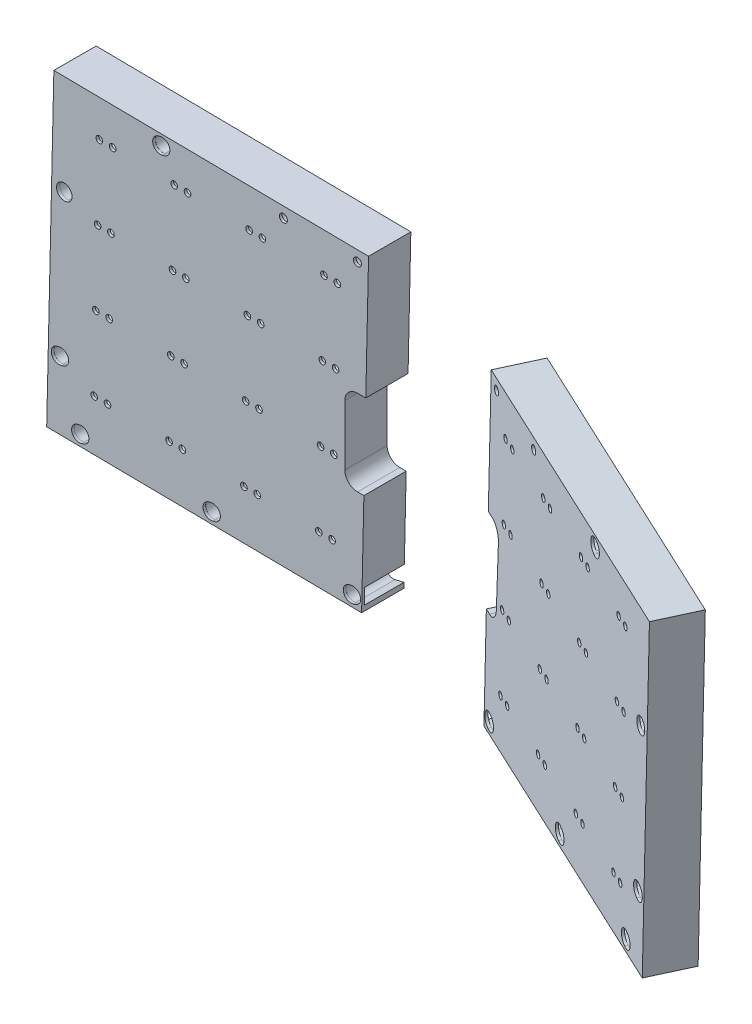
SolidWorks part; units mm, degrees
ref_plane "Front Plane" through (0, 0, 0) normal (0, 0, 1) x (1, 0, 0)
ref_plane "Top Plane" through (0, 0, 0) normal (0, 1, 0) x (1, 0, 0)
ref_plane "Right Plane" through (0, 0, 0) normal (1, 0, 0) x (0, 0, -1)
sketch "Sketch1" plane through (0, 0, 0) normal (0, 0, 1) x (1, 0, 0)
  line L11 (99.4099, -219.1387) -> (-89.6592, -216.966)
  line L12 (-89.6592, -216.966) -> (-93.9705, -404.5237)
  line L13 (-93.9705, -404.5237) -> (95.2285, -406.698)
  line L14 (95.2285, -406.698) -> (99.4099, -219.1387)
  line L21 (95.5423, -393.9824) -> (99.1392, -231.8547)
  line L22 (95.2501, -406.6982) -> (95.5423, -393.9824)
  line L23 (-93.9489, -404.524) -> (95.2501, -406.6982)
  line L24 (-89.6377, -216.9662) -> (-93.9489, -404.524)
  line L25 (99.4315, -219.139) -> (-89.6377, -216.9662)
  line L26 (99.1392, -231.8547) -> (99.4315, -219.139)
  line L27 (95.5423, -393.9824) -> (99.1392, -231.8547)
  line L28 (95.2501, -406.6982) -> (95.5423, -393.9824)
  line L29 (-93.9489, -404.524) -> (95.2501, -406.6982)
  line L30 (-89.6377, -216.9662) -> (-93.9489, -404.524)
  line L31 (99.4315, -219.139) -> (-89.6377, -216.9662)
  line L32 (99.1392, -231.8547) -> (99.4315, -219.139)
  circle A0 centre (80.6426, -242.5843) radius 2 construction
  circle A1 centre (72.6447, -242.4004) radius 2 construction
  circle A2 centre (35.6545, -241.5501) radius 2 construction
  circle A3 centre (27.6566, -241.3663) radius 2 construction
  circle A4 centre (-9.3336, -240.516) radius 2 construction
  circle A5 centre (-17.3315, -240.3322) radius 2 construction
  circle A6 centre (-54.3218, -239.4819) radius 2 construction
  circle A7 centre (-62.3197, -239.2981) radius 2 construction
  circle A8 centre (-63.3538, -284.2862) radius 2 construction
  circle A9 centre (-55.3559, -284.47) radius 2 construction
  circle A10 centre (-18.3657, -285.3203) radius 2 construction
  circle A11 centre (-10.3678, -285.5041) radius 2 construction
  circle A12 centre (26.6225, -286.3544) radius 2 construction
  circle A13 centre (34.6204, -286.5383) radius 2 construction
  circle A14 centre (71.6106, -287.3885) radius 2 construction
  circle A15 centre (79.6085, -287.5724) radius 2 construction
  circle A16 centre (78.5744, -332.5605) radius 2 construction
  circle A17 centre (70.5765, -332.3767) radius 2 construction
  circle A18 centre (33.5862, -331.5264) radius 2 construction
  circle A19 centre (25.5883, -331.3425) radius 2 construction
  circle A20 centre (-11.4019, -330.4923) radius 2 construction
  circle A21 centre (-19.3998, -330.3084) radius 2 construction
  circle A22 centre (-56.39, -329.4581) radius 2 construction
  circle A23 centre (-64.3879, -329.2743) radius 2 construction
  circle A24 centre (-65.422, -374.2624) radius 2 construction
  circle A25 centre (-57.4241, -374.4463) radius 2 construction
  circle A26 centre (-20.4339, -375.2965) radius 2 construction
  circle A27 centre (-12.436, -375.4804) radius 2 construction
  circle A28 centre (24.5542, -376.3307) radius 2 construction
  circle A29 centre (32.5521, -376.5145) radius 2 construction
  circle A30 centre (69.5424, -377.3648) radius 2 construction
  circle A31 centre (77.5402, -377.5486) radius 2 construction
  circle A32 centre (80.6426, -242.5843) radius 2
  circle A33 centre (72.6447, -242.4004) radius 2
  circle A34 centre (35.6545, -241.5501) radius 2
  circle A35 centre (27.6566, -241.3663) radius 2
  circle A36 centre (-9.3336, -240.516) radius 2
  circle A37 centre (-17.3315, -240.3322) radius 2
  circle A38 centre (-54.3218, -239.4819) radius 2
  circle A39 centre (-62.3197, -239.2981) radius 2
  circle A40 centre (-63.3538, -284.2862) radius 2
  circle A41 centre (-55.3559, -284.47) radius 2
  circle A42 centre (-18.3657, -285.3203) radius 2
  circle A43 centre (-10.3678, -285.5041) radius 2
  circle A44 centre (26.6225, -286.3544) radius 2
  circle A45 centre (34.6204, -286.5383) radius 2
  circle A46 centre (71.6106, -287.3885) radius 2
  circle A47 centre (79.6085, -287.5724) radius 2
  circle A48 centre (78.5744, -332.5605) radius 2
  circle A49 centre (70.5765, -332.3767) radius 2
  circle A50 centre (33.5862, -331.5264) radius 2
  circle A51 centre (25.5883, -331.3425) radius 2
  circle A52 centre (-11.4019, -330.4923) radius 2
  circle A53 centre (-19.3998, -330.3084) radius 2
  circle A54 centre (-56.39, -329.4581) radius 2
  circle A55 centre (-64.3879, -329.2743) radius 2
  circle A56 centre (-65.422, -374.2624) radius 2
  circle A57 centre (-57.4241, -374.4463) radius 2
  circle A58 centre (-20.4339, -375.2965) radius 2
  circle A59 centre (-12.436, -375.4804) radius 2
  circle A60 centre (24.5542, -376.3307) radius 2
  circle A61 centre (32.5521, -376.5145) radius 2
  circle A62 centre (69.5424, -377.3648) radius 2
  circle A63 centre (77.5402, -377.5486) radius 2
  ellipse E1 centre (-25.651, -224.0611) end of major axis (-30.0544, -225.5074) minor radius 4.572 construction
  ellipse E2 centre (48.2624, -224.9105) end of major axis (49.7684, -226.8033) minor radius 2.413 construction
  ellipse E3 centre (92.7518, -225.4218) end of major axis (94.2578, -227.3145) minor radius 2.413 construction
  ellipse E4 centre (88.9025, -400.2657) end of major axis (84.3472, -401.3501) minor radius 4.572 construction
  ellipse E5 centre (4.628, -399.2972) end of major axis (0.0728, -400.3817) minor radius 4.572 construction
  ellipse E6 centre (-86.5199, -363.9081) end of major axis (-91.0751, -364.9925) minor radius 4.572 construction
  ellipse E7 centre (-74.3216, -398.39) end of major axis (-78.8768, -399.4744) minor radius 4.572 construction
  ellipse E9 centre (-25.651, -224.0611) end of major axis (-30.0544, -225.5074) minor radius 4.572
  ellipse E10 centre (48.2624, -224.9105) end of major axis (49.7684, -226.8033) minor radius 2.413
  ellipse E11 centre (92.7518, -225.4218) end of major axis (94.2578, -227.3145) minor radius 2.413
  ellipse E12 centre (88.9025, -400.2657) end of major axis (84.3472, -401.3501) minor radius 4.572
  ellipse E13 centre (4.628, -399.2972) end of major axis (0.0728, -400.3817) minor radius 4.572
  ellipse E14 centre (-86.5199, -363.9081) end of major axis (-91.0751, -364.9925) minor radius 4.572
  ellipse E15 centre (-74.3216, -398.39) end of major axis (-78.8768, -399.4744) minor radius 4.572
  dimension "D1" = 0
extrude "Boss-Extrude1" add sketch "Sketch1" against normal blind 1.5875
ref_plane "Plane1" through (-93.9489, -404.524, 5) normal (-0.9999, 0.0115, 0) x (0, 0, 1)
ref_plane "Plane2" through (158.3388, -225.7752, 115.9625) normal (-0.2101, -0.05, 0.9764) x (0.9777, -0.0108, 0.2099)
sketch "Sketch5" plane through (0, 0, -1.5875) normal (0, 0, -1) x (-1, 0, 0)
  line L0 (65.422, -374.2624) -> (57.4241, -374.4463) construction
  line L1 (65.5369, -379.2624) -> (57.539, -379.4463)
  line L2 (65.3071, -369.2624) -> (57.3092, -369.4463)
  line L3 (20.4339, -375.2965) -> (12.436, -375.4804) construction
  line L4 (20.5488, -380.2965) -> (12.5509, -380.4804)
  line L5 (20.319, -370.2965) -> (12.3211, -370.4804)
  line L6 (-24.5542, -376.3307) -> (-32.5521, -376.5145) construction
  line L7 (-24.4393, -381.3307) -> (-32.4372, -381.5145)
  line L8 (-24.6692, -371.3307) -> (-32.6671, -371.5145)
  line L9 (-69.5424, -377.3648) -> (-77.5402, -377.5486) construction
  line L10 (-69.4274, -382.3648) -> (-77.4253, -382.5486)
  line L11 (-69.6573, -372.3648) -> (-77.6552, -372.5486)
  line L12 (64.3879, -329.2743) -> (56.39, -329.4581) construction
  line L13 (64.5028, -334.2746) -> (56.5049, -334.4585)
  line L14 (64.2729, -324.274) -> (56.2751, -324.4578)
  line L15 (19.3998, -330.3084) -> (11.4019, -330.4923) construction
  line L16 (19.5147, -335.3087) -> (11.5168, -335.4926)
  line L17 (19.2848, -325.3081) -> (11.2869, -325.4919)
  line L18 (-25.5883, -331.3425) -> (-33.5862, -331.5264) construction
  line L19 (-25.4734, -336.3425) -> (-33.4713, -336.5264)
  line L20 (-25.7033, -326.3425) -> (-33.7012, -326.5264)
  line L21 (-26.6225, -286.3544) -> (-34.6204, -286.5383) construction
  line L22 (-26.5075, -291.3547) -> (-34.5054, -291.5386)
  line L23 (-26.7374, -281.3541) -> (-34.7353, -281.5379)
  line L24 (18.3657, -285.3203) -> (10.3678, -285.5041) construction
  line L25 (18.4806, -290.3203) -> (10.4827, -290.5041)
  line L26 (18.2507, -280.3203) -> (10.2528, -280.5041)
  line L27 (-70.5765, -332.3767) -> (-78.5744, -332.5605) construction
  line L28 (-70.4615, -337.3767) -> (-78.4594, -337.5605)
  line L29 (-70.6914, -327.3767) -> (-78.6893, -327.5605)
  line L30 (-71.6106, -287.3885) -> (-79.6085, -287.5724) construction
  line L31 (-71.4957, -292.3885) -> (-79.4935, -292.5724)
  line L32 (-71.7255, -282.3885) -> (-79.7234, -282.5724)
  line L33 (-27.6566, -241.3663) -> (-35.6545, -241.5501) construction
  line L34 (-27.5416, -246.3663) -> (-35.5395, -246.5501)
  line L35 (-27.7715, -236.3663) -> (-35.7694, -236.5501)
  line L36 (-72.6447, -242.4004) -> (-80.6426, -242.5843) construction
  line L37 (-72.5298, -247.4004) -> (-80.5277, -247.5843)
  line L38 (-72.7596, -237.4004) -> (-80.7575, -237.5843)
  line L39 (17.3315, -240.3322) -> (9.3336, -240.516) construction
  line L40 (17.4465, -245.3322) -> (9.4486, -245.516)
  line L41 (17.2166, -235.3322) -> (9.2187, -235.516)
  line L42 (62.3197, -239.2981) -> (54.3218, -239.4819) construction
  line L43 (62.4346, -244.2984) -> (54.4367, -244.4822)
  line L44 (62.2047, -234.2977) -> (54.2068, -234.4816)
  line L45 (55.3559, -284.47) -> (63.3538, -284.2862) construction
  line L48 (65.5369, -379.2624) -> (65.3071, -369.2624) construction
  line L49 (20.319, -370.2965) -> (20.5488, -380.2965) construction
  line L50 (-24.4393, -381.3307) -> (-24.6692, -371.3307) construction
  line L51 (-69.6573, -372.3648) -> (-69.4274, -382.3648) construction
  line L52 (-70.4615, -337.3767) -> (-70.6914, -327.3767) construction
  line L53 (-25.4734, -336.3425) -> (-25.7033, -326.3425) construction
  line L54 (19.5147, -335.3087) -> (19.3998, -325.3068) construction
  line L55 (64.5028, -334.2746) -> (64.3879, -324.2727) construction
  line L57 (62.4346, -244.2984) -> (62.3197, -234.2964) construction
  line L58 (17.4465, -245.3322) -> (17.2166, -235.3322) construction
  line L59 (18.4806, -290.3203) -> (18.2507, -280.3203) construction
  line L60 (-26.5075, -291.3547) -> (-26.6225, -281.3528) construction
  line L61 (-27.5416, -246.3663) -> (-27.7715, -236.3663) construction
  line L62 (-71.4957, -292.3885) -> (-71.7255, -282.3885) construction
  line L63 (-72.5298, -247.4004) -> (-72.7596, -237.4004) construction
  line L64 (93.9489, -404.524) -> (-95.2285, -406.698) construction
  line L66 (-99.4099, -219.1387) -> (89.6377, -216.9662) construction
  line L67 (-95.2285, -406.698) -> (-99.4099, -219.1387) construction
  line L68 (55.2409, -279.47) -> (63.2388, -279.2862)
  line L70 (93.9489, -404.524) -> (-95.2285, -406.698)
  line L72 (-99.4099, -219.1387) -> (89.6377, -216.9662)
  line L73 (-95.2285, -406.698) -> (-99.4099, -219.1387)
  line L74 (-99.4099, -219.1387) -> (-99.1176, -231.8545)
  line L75 (55.4708, -289.47) -> (63.4687, -289.2862)
  arc A0 (65.5369, -379.2624) -> (65.3071, -369.2624) centre (65.422, -374.2624) ccw
  arc A1 (57.3092, -369.4463) -> (57.539, -379.4463) centre (57.4241, -374.4463) ccw
  arc A2 (20.5488, -380.2965) -> (20.319, -370.2965) centre (20.4339, -375.2965) ccw
  arc A3 (12.3211, -370.4804) -> (12.5509, -380.4804) centre (12.436, -375.4804) ccw
  arc A4 (-24.4393, -381.3307) -> (-24.6692, -371.3307) centre (-24.5542, -376.3307) ccw
  arc A5 (-32.6671, -371.5145) -> (-32.4372, -381.5145) centre (-32.5521, -376.5145) ccw
  arc A6 (-69.4274, -382.3648) -> (-69.6573, -372.3648) centre (-69.5424, -377.3648) ccw
  arc A7 (-77.6552, -372.5486) -> (-77.4253, -382.5486) centre (-77.5402, -377.5486) ccw
  arc A8 (64.5028, -334.2746) -> (64.2729, -324.274) centre (64.3879, -329.2743) ccw
  arc A9 (56.2751, -324.4578) -> (56.5049, -334.4585) centre (56.39, -329.4581) ccw
  arc A10 (19.5147, -335.3087) -> (19.2848, -325.3081) centre (19.3998, -330.3084) ccw
  arc A11 (11.2869, -325.4919) -> (11.5168, -335.4926) centre (11.4019, -330.4923) ccw
  arc A12 (-25.4734, -336.3425) -> (-25.7033, -326.3425) centre (-25.5883, -331.3425) ccw
  arc A13 (-33.7012, -326.5264) -> (-33.4713, -336.5264) centre (-33.5862, -331.5264) ccw
  arc A14 (-26.5075, -291.3547) -> (-26.7374, -281.3541) centre (-26.6225, -286.3544) ccw
  arc A15 (-34.7353, -281.5379) -> (-34.5054, -291.5386) centre (-34.6204, -286.5383) ccw
  arc A16 (18.4806, -290.3203) -> (18.2507, -280.3203) centre (18.3657, -285.3203) ccw
  arc A17 (10.2528, -280.5041) -> (10.4827, -290.5041) centre (10.3678, -285.5041) ccw
  arc A18 (-70.4615, -337.3767) -> (-70.6914, -327.3767) centre (-70.5765, -332.3767) ccw
  arc A19 (-78.6893, -327.5605) -> (-78.4594, -337.5605) centre (-78.5744, -332.5605) ccw
  arc A20 (-71.4957, -292.3885) -> (-71.7255, -282.3885) centre (-71.6106, -287.3885) ccw
  arc A21 (-79.7234, -282.5724) -> (-79.4935, -292.5724) centre (-79.6085, -287.5724) ccw
  arc A22 (-27.5416, -246.3663) -> (-27.7715, -236.3663) centre (-27.6566, -241.3663) ccw
  arc A23 (-35.7694, -236.5501) -> (-35.5395, -246.5501) centre (-35.6545, -241.5501) ccw
  arc A24 (-72.5298, -247.4004) -> (-72.7596, -237.4004) centre (-72.6447, -242.4004) ccw
  arc A25 (-80.7575, -237.5843) -> (-80.5277, -247.5843) centre (-80.6426, -242.5843) ccw
  arc A26 (17.4465, -245.3322) -> (17.2166, -235.3322) centre (17.3315, -240.3322) ccw
  arc A27 (9.2187, -235.516) -> (9.4486, -245.516) centre (9.3336, -240.516) ccw
  arc A28 (62.4346, -244.2984) -> (62.2047, -234.2977) centre (62.3197, -239.2981) ccw
  arc A29 (54.2068, -234.4816) -> (54.4367, -244.4822) centre (54.3218, -239.4819) ccw
  circle A32 centre (-92.7302, -225.4215) radius 5.08
  circle A33 centre (-48.2408, -224.9103) radius 5.08
  arc A36 (55.2409, -279.47) -> (55.4708, -289.47) centre (55.3559, -284.47) ccw
  arc A37 (63.4687, -289.2862) -> (63.2388, -279.2862) centre (63.3538, -284.2862) ccw
  point P4 (61.4231, -374.3543)
  point P13 (16.4349, -375.3885)
  point P18 (-28.5532, -376.4226)
  point P27 (-73.5413, -377.4567)
  point P36 (60.3889, -329.3662)
  point P45 (15.4008, -330.4003)
  point P54 (-29.5873, -331.4345)
  point P63 (-30.6214, -286.4463)
  point P72 (14.3667, -285.4122)
  point P83 (-74.5754, -332.4686)
  point P90 (-75.6095, -287.4805)
  point P99 (-31.6555, -241.4582)
  point P108 (-76.6436, -242.4923)
  point P117 (13.3326, -240.4241)
  point P126 (58.3207, -239.39)
  point P137 (59.3548, -284.3781)
  dimension "D1" = 10.16
  dimension "D2" = 10
  dimension "D3" = 10
extrude "Boss-Extrude2" add sketch "Sketch5" along normal blind 23.8125
ref_plane "Plane3" through (-8.4003, -1.9998, 39.0332) normal (0.2101, 0.05, -0.9764) x (-0.9777, 0.0108, -0.2099)
sketch "Sketch6" plane through (-8.4003, -1.9998, 39.0332) normal (0.2101, 0.05, -0.9764) x (-0.9777, 0.0108, -0.2099)
  circle A0 centre (79.6264, -363.1756) radius 4.572 construction
  circle A1 centre (67.3297, -397.6123) radius 4.572 construction
  circle A2 centre (-9.8669, -398.5184) radius 4.572 construction
  circle A3 centre (-92.2703, -399.4856) radius 4.572 construction
  circle A4 centre (79.6264, -363.1756) radius 4.572
  circle A5 centre (67.3297, -397.6123) radius 4.572
  circle A6 centre (-9.8669, -398.5184) radius 4.572
  circle A7 centre (-92.2703, -399.4856) radius 4.572
  ellipse E0 centre (21.6201, -223.5118) end of major axis (21.0178, -228.045) minor radius 4.5244 construction
  ellipse E2 centre (21.6201, -223.5118) end of major axis (21.0178, -228.045) minor radius 4.5244
  ellipse E5 centre (78.5604, -276.6847) end of major axis (81.3617, -272.8961) minor radius 4.4898 construction
  ellipse E6 centre (78.5604, -276.6847) end of major axis (81.3617, -272.8961) minor radius 4.4898
extrude "Cut-Extrude1" cut sketch "Sketch6" along normal through all
sketch "Sketch7" plane through (0, 0, -25.4) normal (0, 0, -1) x (-1, 0, 0)
  line L0 (-99.4099, -219.1387) -> (-95.5086, -394.1302) construction
  line L1 (-97.7478, -293.692) -> (-85.1672, -293.692)
  line L2 (-97.7478, -293.692) -> (-97.7478, -345.0444)
  line L3 (-97.7478, -345.0444) -> (-85.1672, -345.0444)
  line L4 (-85.1672, -293.692) -> (-85.1672, -345.0444)
extrude "Cut-Extrude2" cut sketch "Sketch7" against normal through all
ref_plane "Plane4" through (-79.8788, 1.8361, -17.0966) normal (-0.9776, 0.0225, -0.2092) x (-0.2092, 0.0048, 0.9779)
ref_plane "Plane5" through (146.7059, -3.3722, 31.3997) normal (-0.9776, 0.0225, -0.2092) x (-0.2092, 0.0048, 0.9779)
sketch "Sketch8" plane through (0, 0, -25.4) normal (0, 0, -1) x (-1, 0, 0)
  line L0 (-95.4448, -398.7082) -> (-88.9025, -400.2657) construction
  line L1 (-94.3684, -394.1867) -> (-87.8261, -395.7442)
  line L2 (-96.5212, -403.2298) -> (-89.9789, -404.7872)
  line L3 (-4.628, -399.2972) -> (-11.1704, -397.7398) construction
  line L4 (-5.698, -403.7917) -> (-12.2403, -402.2343)
  line L5 (-3.5581, -394.8027) -> (-10.1004, -393.2453)
  line L6 (67.7792, -396.8325) -> (74.3216, -398.39) construction
  line L7 (68.8814, -392.2027) -> (75.4237, -393.7602)
  line L8 (66.677, -401.4623) -> (73.2194, -403.0198)
  line L9 (79.9775, -362.3507) -> (86.5199, -363.9081) construction
  line L10 (81.0454, -357.8647) -> (87.5878, -359.4222)
  line L11 (78.9096, -366.8366) -> (85.4519, -368.3941)
  line L12 (19.1086, -222.5036) -> (25.651, -224.0611) construction
  line L13 (20.1609, -218.0834) -> (26.7033, -219.6409)
  line L14 (18.0563, -226.9239) -> (24.5987, -228.4813)
  line L15 (77.9348, -275.7463) -> (83.4011, -277.0476) construction
  line L16 (79.0178, -271.197) -> (84.4841, -272.4983)
  line L17 (76.8518, -280.2955) -> (82.3181, -281.5968)
  arc A0 (-94.3684, -394.1867) -> (-96.5212, -403.2298) centre (-95.4448, -398.7082) ccw
  arc A1 (-89.9789, -404.7872) -> (-87.8261, -395.7442) centre (-88.9025, -400.2657) ccw
  arc A2 (-5.698, -403.7917) -> (-3.5581, -394.8027) centre (-4.628, -399.2972) ccw
  arc A3 (-10.1004, -393.2453) -> (-12.2403, -402.2343) centre (-11.1704, -397.7398) ccw
  arc A4 (68.8814, -392.2027) -> (66.677, -401.4623) centre (67.7792, -396.8325) ccw
  arc A5 (73.2194, -403.0198) -> (75.4237, -393.7602) centre (74.3216, -398.39) ccw
  arc A6 (81.0454, -357.8647) -> (78.9096, -366.8366) centre (79.9775, -362.3507) ccw
  arc A7 (85.4519, -368.3941) -> (87.5878, -359.4222) centre (86.5199, -363.9081) ccw
  arc A8 (20.1609, -218.0834) -> (18.0563, -226.9239) centre (19.1086, -222.5036) ccw
  arc A9 (24.5987, -228.4813) -> (26.7033, -219.6409) centre (25.651, -224.0611) ccw
  arc A10 (79.0178, -271.197) -> (76.8518, -280.2955) centre (77.9348, -275.7463) ccw
  arc A11 (82.3181, -281.5968) -> (84.4841, -272.4983) centre (83.4011, -277.0476) ccw
  ellipse E0 centre (77.9348, -275.7463) end of major axis (81.585, -272.7241) minor radius 4.572 construction
  ellipse E7 centre (83.4011, -277.0476) end of major axis (87.0513, -274.0254) minor radius 4.572 construction
  point P2 (-92.1736, -399.487)
  point P7 (-7.8992, -398.5185)
  point P14 (71.0504, -397.6112)
  point P21 (83.2487, -363.1294)
  point P30 (22.3798, -223.2824)
  point P37 (80.6679, -276.3969)
  point P42 (82.2928, -275.3875)
  point P43 (76.8264, -274.0862)
  point P44 (75.7262, -269.7324)
  point P51 (82.5088, -277.7)
  point P52 (76.7176, -281.2607)
extrude "Cut-Extrude3" cut sketch "Sketch8" against normal blind 23.8125
fillet "Fillet1" radius 7.62 2 edges at (85.1672, -293.692, -12.7) (85.1672, -345.0444, -12.7)
mirror "Mirror2" about plane through (146.7059, -3.3722, 31.3997) normal (-0.9776, 0.0225, -0.2092) of bodies 110 108
